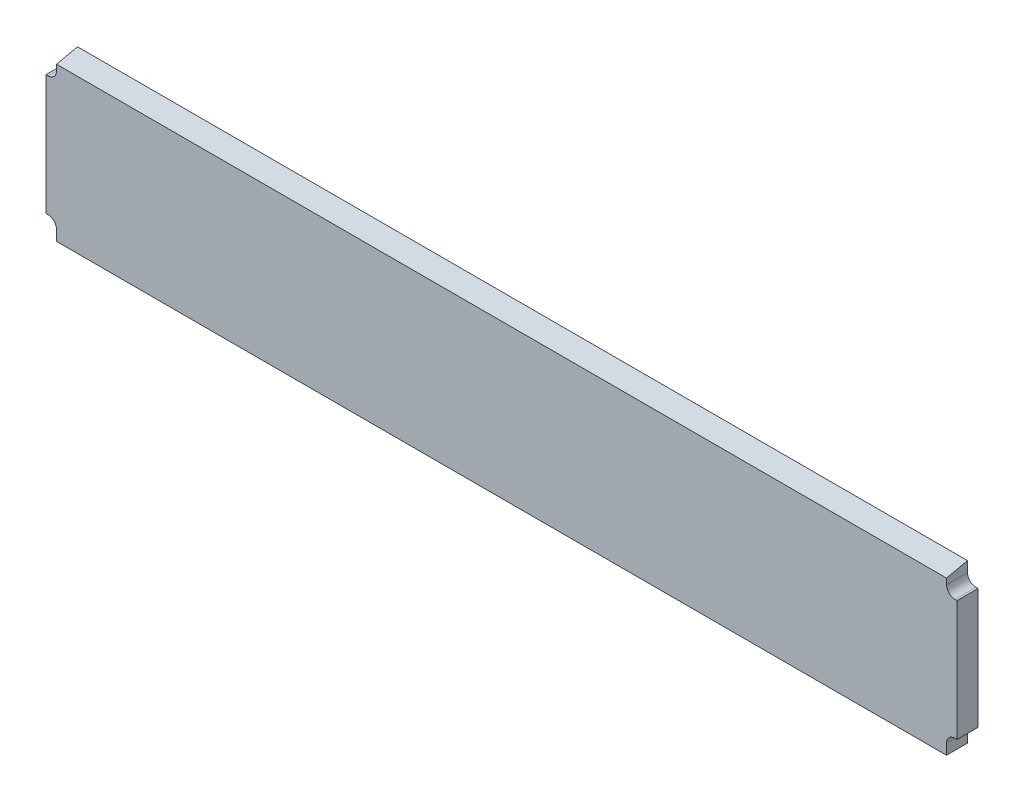
SolidWorks part; units mm, degrees
ref_plane "Front Plane" through (0, 0, 0) normal (0, 0, 1) x (1, 0, 0)
ref_plane "Top Plane" through (0, 0, 0) normal (0, 1, 0) x (1, 0, 0)
ref_plane "Right Plane" through (0, 0, 0) normal (1, 0, 0) x (0, 0, -1)
sketch "Sketch1" plane through (0, 0, 0) normal (0, 0, 1) x (1, 0, 0)
  line L0 (-336.55, -45.4914) -> (-336.55, -59.7789)
  line L1 (336.55, 59.7789) -> (-336.55, 59.7789)
  line L2 (336.55, 59.7789) -> (336.55, 45.4914)
  line L3 (336.55, -59.7789) -> (-336.55, -59.7789)
  line L4 (-336.55, 59.7789) -> (-336.55, 45.4914)
  line L5 (336.55, 59.7789) -> (-336.55, -59.7789) construction
  line L6 (336.55, -59.7789) -> (-336.55, 59.7789) construction
  line L7 (344.4875, 45.4914) -> (336.55, 45.4914)
  line L8 (344.4875, 45.4914) -> (344.4875, -45.4914)
  line L9 (344.4875, -45.4914) -> (336.55, -45.4914)
  line L10 (-344.4875, 45.4914) -> (-344.4875, -45.4914)
  line L11 (344.4875, 45.4914) -> (-344.4875, -45.4914) construction
  line L12 (344.4875, -45.4914) -> (-344.4875, 45.4914) construction
  line L13 (336.55, -45.4914) -> (336.55, -59.7789)
  line L14 (-336.55, 45.4914) -> (-344.4875, 45.4914)
  line L15 (-336.55, -45.4914) -> (-344.4875, -45.4914)
  point P0 (0, 0)
  point P6 (0, 0)
  dimension "D1" = 673.1
  dimension "D2" = 119.5578
  dimension "D3" = 7.9375
  dimension "D4" = 14.2875
  dimension "D5" = 688.975
extrude "Boss-Extrude1" add sketch "Sketch1" along normal blind 15.875 contours L1 L4 L14 L10 L15 L0 L3 L13 L9 L8 L7 L2
fillet "Fillet1" radius 6.35 4 edges at (-336.55, -45.4914, 7.9375) (-336.55, 45.4914, 7.9375) (336.55, -45.4914, 7.9375) (336.55, 45.4914, 7.9375)
sketch "Sketch2" plane through (344.4875, 0, 0) normal (1, 0, 0) x (0, 0, -1)
  line L7 (0, 59.7789) -> (-15.875, 56.2595)
  line L8 (-15.875, 59.7789) -> (-15.875, 51.8414) construction
  line L9 (-15.875, 56.2595) -> (-15.875, 59.7789)
  line L10 (-15.875, 59.7789) -> (0, 59.7789)
  dimension "D1" = 12.5
extrude "Cut-Extrude1" cut sketch "Sketch2" against normal through all both and the other way through all
